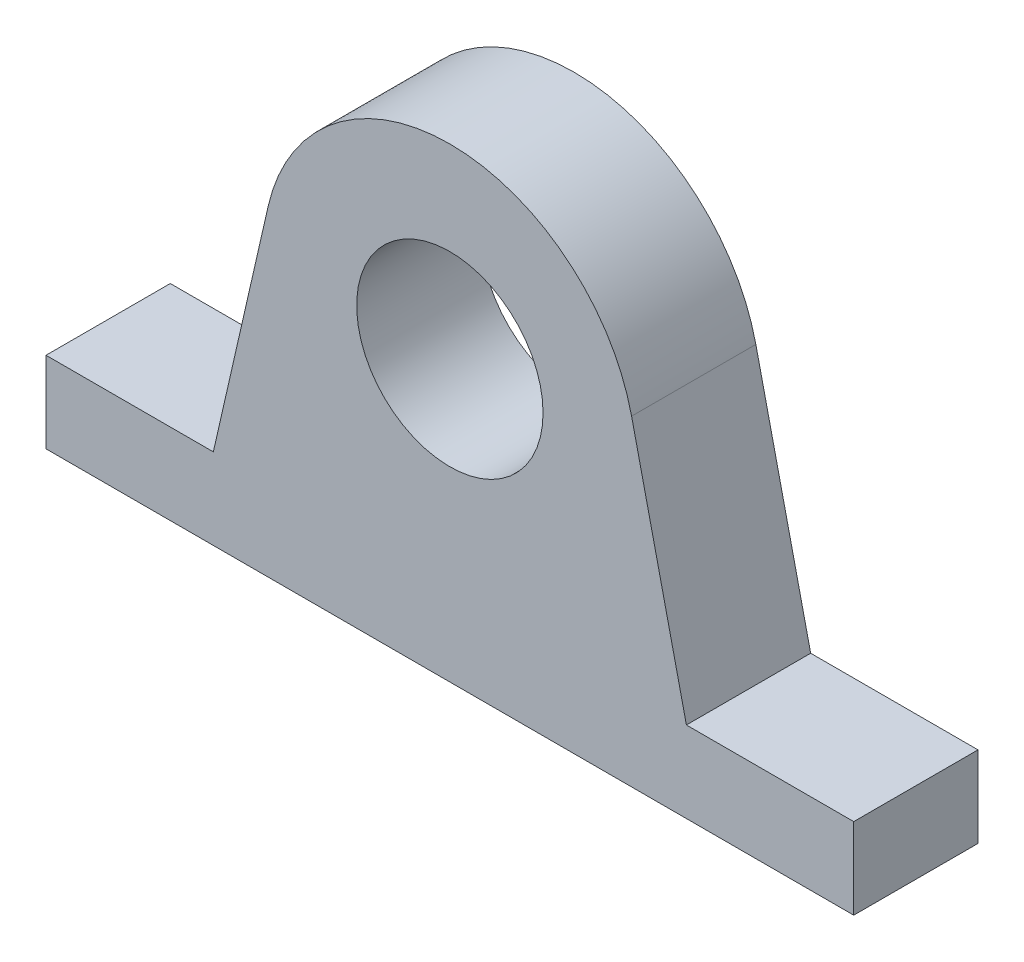
SolidWorks part; units mm, degrees
ref_plane "Plano frontal" through (0, 0, 0) normal (0, 0, 1) x (1, 0, 0)
ref_plane "Plano superior" through (0, 0, 0) normal (0, 1, 0) x (1, 0, 0)
ref_plane "Plano direito" through (0, 0, 0) normal (1, 0, 0) x (0, 0, -1)
sketch "Esboço1" plane through (0, 0, 0) normal (0, 0, 1) x (1, 0, 0)
  line L0 (-8.2096, 0) -> (8.2096, 0)
  line L1 (-7.6138, 2.6092) -> (-5.8494, 10.3357)
  line L2 (7.6138, 2.6092) -> (5.8494, 10.3357)
  line L3 (-8.2096, 0) -> (-13, 0)
  line L4 (-13, 0) -> (-13, 2.6092)
  line L5 (-13, 2.6092) -> (-7.6138, 2.6092)
  line L6 (0, 0) -> (0, 9) construction
  line L7 (13, 2.6092) -> (7.6138, 2.6092)
  line L8 (13, 0) -> (13, 2.6092)
  line L9 (8.2096, 0) -> (13, 0)
  circle A0 centre (0, 9) radius 3
  arc A1 (5.8494, 10.3357) -> (-5.8494, 10.3357) centre (0, 9) ccw
  point P2 (0, 8.5772)
  point P7 (0, 0)
  dimension "D1" = 9
  dimension "D2" = 6
  dimension "D4" = 6
  dimension "D3" = 13
extrude "Ressalto-extrusão1" add sketch "Esboço1" along normal blind 4
